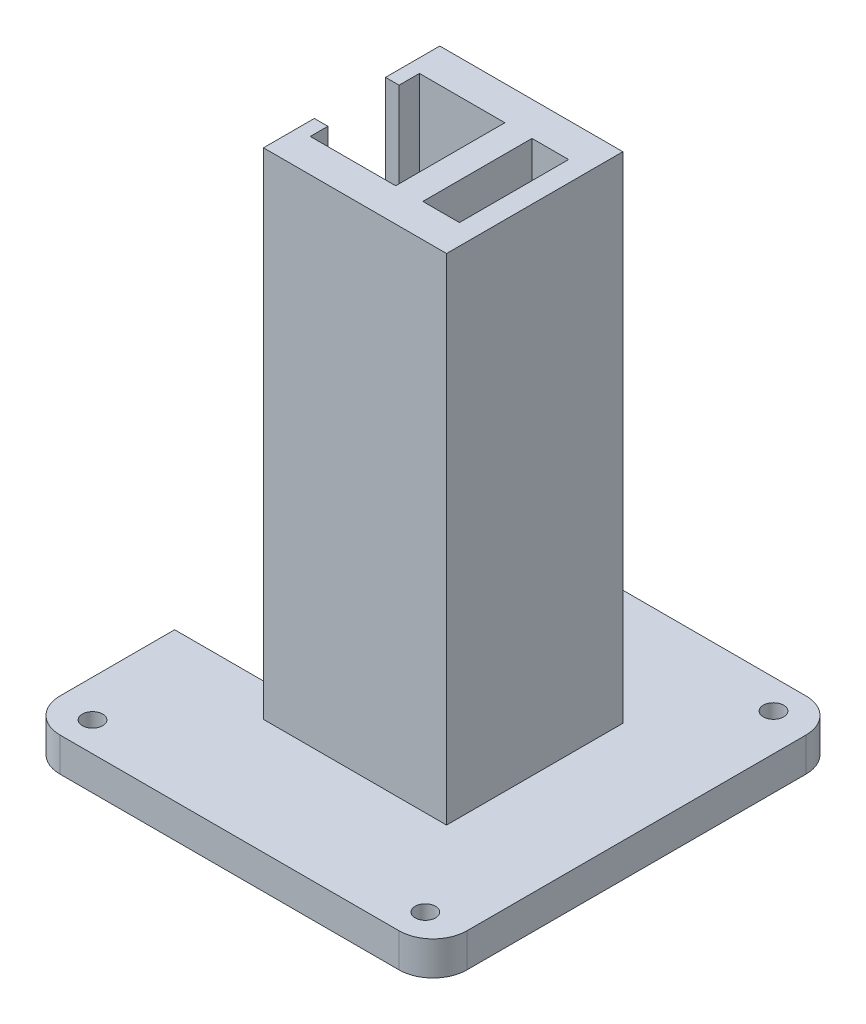
SolidWorks part; units mm, degrees
ref_plane "Front Plane" through (0, 0, 0) normal (0, 0, 1) x (1, 0, 0)
ref_plane "Top Plane" through (0, 0, 0) normal (0, 1, 0) x (1, 0, 0)
ref_plane "Right Plane" through (0, 0, 0) normal (1, 0, 0) x (0, 0, -1)
sketch "Sketch1" plane through (0, 0, 0) normal (0, 0, 1) x (1, 0, 0)
  line L1 (15, -36.5) -> (-15, -36.5)
  line L2 (15, -36.5) -> (15, 36.5)
  line L3 (15, 36.5) -> (-15, 36.5)
  line L4 (-15, -36.5) -> (-15, 36.5)
  line L5 (15, -36.5) -> (-15, 36.5) construction
  line L6 (15, 36.5) -> (-15, -36.5) construction
  point P0 (0, 0)
  dimension "D1" = 30
  dimension "D2" = 73
extrude "Boss-Extrude1" add sketch "Sketch1" along normal blind 26
sketch "Sketch2" plane through (0, 36.5, 0) normal (0, 1, 0) x (1, 0, 0)
  line L0 (-15, -26) -> (-15, 0) construction
  line L1 (-13, -5) -> (12, -5)
  line L2 (-13, -5) -> (-13, -21.1)
  line L3 (-13, -21.1) -> (12, -21.1)
  line L4 (12, -5) -> (12, -21.1)
  line L5 (15, 0) -> (-15, 0) construction
  line L6 (15, -26) -> (15, 0) construction
  dimension "D1" = 2
  dimension "D2" = 5
  dimension "D3" = 16.1
  dimension "D4" = 3
extrude "Cut-Extrude1" cut sketch "Sketch2" against normal through all
sketch "Sketch3" plane through (-15, 0, 0) normal (-1, 0, 0) x (0, 0, 1)
  line L0 (0, 36.5) -> (0, -36.5) construction
  line L1 (0, 33.5) -> (26, 33.5)
  line L2 (0, 33.5) -> (0, 9.5)
  line L3 (0, 9.5) -> (26, 9.5)
  line L4 (26, 33.5) -> (26, 9.5)
  line L5 (26, 36.5) -> (26, -36.5) construction
  line L6 (26, 36.5) -> (0, 36.5) construction
  line L8 (0, 6.5) -> (26, 6.5)
  line L9 (0, 6.5) -> (0, -17.5)
  line L10 (0, -17.5) -> (26, -17.5)
  line L11 (26, 6.5) -> (26, -17.5)
  line L12 (0, -20.5) -> (26, -20.5)
  line L13 (0, -20.5) -> (0, -36.7342)
  line L14 (0, -36.7342) -> (26, -36.7342)
  line L15 (26, -20.5) -> (26, -36.7342)
  dimension "D1" = 3
  dimension "D2" = 24
  dimension "D3" = 3
  dimension "D4" = 3
  dimension "D5" = 24
extrude "Cut-Extrude2" cut sketch "Sketch3" against normal blind 5
ref_plane "Plane1" through (0, -36.5, 0) normal (0, -1, 0) x (-1, 0, 0)
sketch "Sketch5" plane through (0, -36.5, 0) normal (0, -1, 0) x (-1, 0, 0)
  line L0 (0, 0) -> (0, -31.2349) construction
  line L1 (-15, -13) -> (15, -13) construction
  line L2 (-15, -26) -> (-15, 0) construction
  line L3 (15, -26) -> (15, 0) construction
  line L5 (30, -43) -> (-30, -43)
  line L6 (30, -43) -> (30, 17)
  line L7 (30, 17) -> (-30, 17)
  line L8 (-30, -43) -> (-30, 17)
  line L9 (30, -43) -> (-30, 17) construction
  line L10 (30, 17) -> (-30, -43) construction
  point P9 (0, -13)
  dimension "D1" = 60
  dimension "D2" = 60
extrude "Boss-Extrude2" add sketch "Sketch5" along normal blind 5
fillet "Fillet1" radius 5 4 edges at (-30, -39, -17) (30, -39, -17) (30, -39, 43) (-30, -39, 43)
sketch "Sketch6" plane through (0, -36.5, 0) normal (0, 1, 0) x (1, 0, 0)
  line L0 (0, 17) -> (0, -43) construction
  line L1 (-25, 17) -> (25, 17) construction
  line L2 (25, -43) -> (-25, -43) construction
  line L3 (-30, -13) -> (43.9834, -13) construction
  line L4 (-30, -38) -> (-30, 12) construction
  circle A0 centre (-24.5405, 12.6715) radius 1.5
  circle A1 centre (24.5405, 12.6715) radius 1.5
  circle A2 centre (-24.5405, -38.6715) radius 1.5
  circle A3 centre (24.5405, -38.6715) radius 1.5
  dimension "D1" = 3
extrude "Cut-Extrude4" cut sketch "Sketch6" against normal blind 5
sketch "Sketch7" plane through (0, 0, 0) normal (0, 0, -1) x (-1, 0, 0)
  line L0 (-15, 36.5) -> (15, 36.5) construction
  line L1 (-15, -36.5) -> (-15, 36.5) construction
  circle A0 centre (-7, 31.5) radius 1
  circle A1 centre (-12, 24.5) radius 1
  circle A2 centre (-2, 24.5) radius 1
  circle A3 centre (-7, 18.5) radius 1
  dimension "D1" = 2
  dimension "D2" = 5
  dimension "D4" = 2
  dimension "D7" = 2
  dimension "D8" = 12
  dimension "D9" = 13
  dimension "D10" = 2
  dimension "D3" = 8
  dimension "D5" = 12
  dimension "D6" = 3
  dimension "D11" = 8
  dimension "D12" = 18
extrude "Cut-Extrude5" cut sketch "Sketch7" against normal blind 4
sketch "Sketch8" plane through (-30, 0, 0) normal (-1, 0, 0) x (0, 0, 1)
  line L0 (38, -41.5) -> (-12, -41.5) construction
  line L1 (5, -36.5) -> (20.5, -36.5)
  line L2 (5, -36.5) -> (5, -41.5)
  line L3 (5, -41.5) -> (20.5, -41.5)
  line L4 (20.5, -36.5) -> (20.5, -41.5)
  line L5 (38, -36.5) -> (-12, -36.5) construction
  line L6 (21.1, -36.5) -> (5, -36.5) construction
extrude "Cut-Extrude6" cut sketch "Sketch8" against normal blind 42
sketch "Sketch9" plane through (0, 36.5, 0) normal (0, 1, 0) x (1, 0, 0)
  line L0 (15, -26) -> (-15, -26) construction
  line L1 (-15, 0) -> (-10, 0)
  line L2 (-15, 0) -> (-15, -26)
  line L3 (-15, -26) -> (-10, -26)
  line L4 (-10, 0) -> (-10, -26)
  dimension "D1" = 5
extrude "Cut-Extrude7" cut sketch "Sketch9" against normal blind 73
ref_plane "Plane2" through (0, 36.5, 0) normal (0, 1, 0) x (1, 0, 0)
sketch "Sketch10" plane through (0, 36.5, 0) normal (0, 1, 0) x (1, 0, 0)
  line L0 (-10, 0) -> (-12, 0)
  line L1 (15, 0) -> (-15, 0) construction
  line L2 (-12, 0) -> (-12, -8)
  line L3 (-12, -8) -> (-10, -8)
  line L4 (-10, -8) -> (-10, 0)
  line L5 (-10, -26) -> (-12, -26)
  line L6 (-12, -26) -> (-12, -18.5)
  line L7 (-12, -18.5) -> (-10, -18.5)
  line L8 (-10, -18.5) -> (-10, -26)
  dimension "D1" = 2
  dimension "D2" = 8
  dimension "D3" = 2
  dimension "D4" = 7.5
extrude "Boss-Extrude3" add sketch "Sketch10" against normal blind 78
sketch "Sketch11" plane through (0, -36.5, 0) normal (0, 1, 0) x (1, 0, 0)
  line L0 (12, -20.5) -> (12, -21.1)
  line L1 (12, -21.1) -> (-30, -21.1)
  line L2 (-30, -38) -> (-30, -20.5) construction
  line L3 (-30, -21.1) -> (-30, -20.5)
  line L4 (-30, -20.5) -> (12, -20.5)
extrude "Cut-Extrude8" cut sketch "Sketch11" against normal through all
ref_plane "Plane4" through (-12, 0, 0) normal (-1, 0, 0) x (0, 0, 1)
sketch "Sketch13" plane through (-12, 0, 0) normal (-1, 0, 0) x (0, 0, 1)
  line L0 (20.5, -36.5) -> (21.1, -36.5)
  line L1 (21.1, -36.5) -> (21.1, -41.5)
  line L2 (21.1, -41.5) -> (20.5, -41.5)
  line L3 (20.5, -41.5) -> (20.5, -36.5)
extrude "Boss-Extrude5" add sketch "Sketch13" against normal blind 2
sketch "Sketch15" plane through (0, 36.5, 0) normal (0, 1, 0) x (1, 0, 0)
  line L0 (2.6, -5) -> (2.6, -21.1)
  line L1 (12, -5) -> (-10, -5) construction
  line L2 (-10, -21.1) -> (12, -21.1) construction
  line L3 (2.6, -21.1) -> (6.6, -21.1)
  line L5 (6.6, -5) -> (2.6, -5)
  line L6 (6.6, -5) -> (6.6, -21.1)
  dimension "D2" = 4
extrude "Boss-Extrude6" add sketch "Sketch15" against normal blind 78
